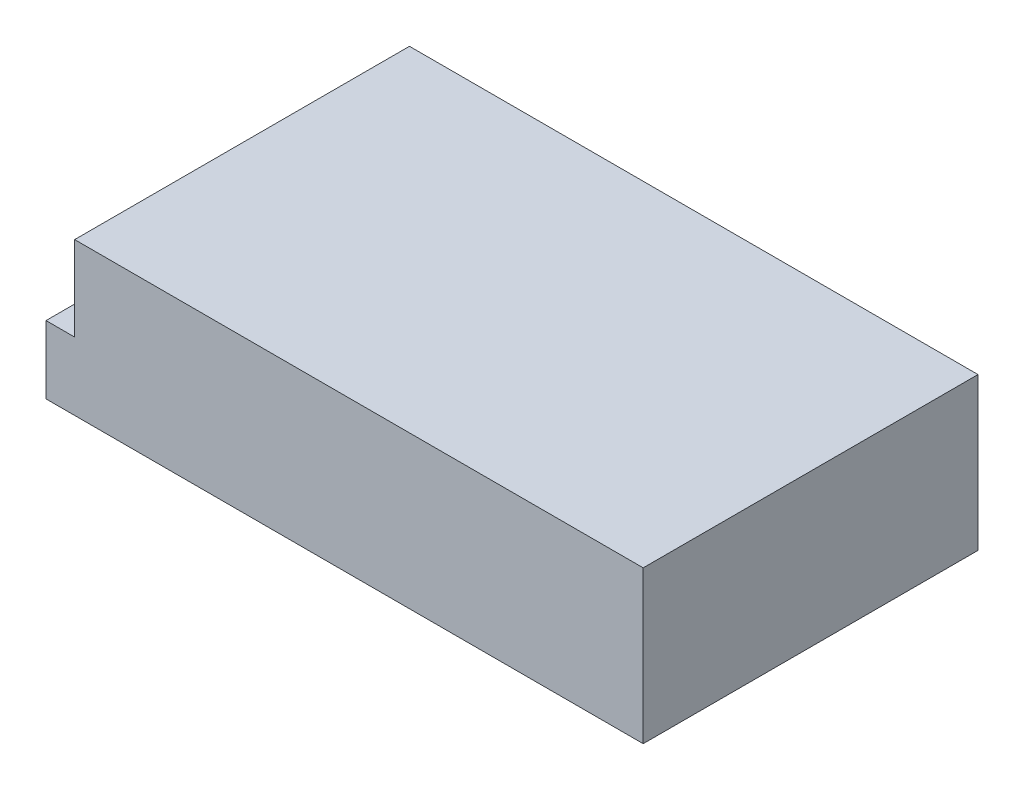
SolidWorks part; units mm, degrees
ref_plane "Front Plane" through (0, 0, 0) normal (0, 0, 1) x (1, 0, 0)
ref_plane "Top Plane" through (0, 0, 0) normal (0, 1, 0) x (1, 0, 0)
ref_plane "Right Plane" through (0, 0, 0) normal (1, 0, 0) x (0, 0, -1)
sketch "Sketch1" plane through (0, 0, 0) normal (0, 1, 0) x (1, 0, 0)
  line L0 (0, 41.5383) -> (0, -45.9656) construction
  line L1 (-99, 55.5) -> (99, 55.5)
  line L2 (-99, 55.5) -> (-99, -55.5)
  line L3 (-99, -55.5) -> (99, -55.5)
  line L4 (99, 55.5) -> (99, -55.5)
  line L5 (-77.8681, 0) -> (67.7114, 0) construction
  dimension "D1" = 198
  dimension "D2" = 111
extrude "Boss-Extrude1" add sketch "Sketch1" along normal blind 50.5
sketch "Sketch2" plane through (0, 0, -55.5) normal (0, 0, -1) x (-1, 0, 0)
  line L0 (-99, 50.5) -> (99, 50.5) construction
  line L1 (89.5, 50.5) -> (99, 50.5)
  line L2 (89.5, 50.5) -> (89.5, 22.5)
  line L3 (89.5, 22.5) -> (99, 22.5)
  line L4 (99, 50.5) -> (99, 22.5)
  line L5 (99, 50.5) -> (99, 0) construction
  dimension "D1" = 28
  dimension "D2" = 9.5
extrude "Cut-Extrude1" cut sketch "Sketch2" against normal blind 147.5
sketch "Sketch4" plane through (0, 0, 0) normal (0, -1, 0) x (1, 0, 0)
  line L0 (87, 68.5931) -> (87, -70.457) construction
  line L2 (99, 55.5) -> (99, -55.5) construction
  line L3 (108.8775, -45.5) -> (-114.4936, -45.5) construction
  line L4 (99, -55.5) -> (-99, -55.5) construction
  line L5 (111.0581, 39.5) -> (-119.8441, 39.5) construction
  line L6 (-99, 55.5) -> (99, 55.5) construction
  circle A0 centre (87, 39.5) radius 1.5
  circle A1 centre (87, -45.5) radius 1.5
  circle A2 centre (-39, 39.5) radius 1.5
  circle A3 centre (-39, -45.5) radius 1.5
  dimension "D3" = 3
  dimension "D1" = 12
  dimension "D2" = 10
  dimension "D4" = 16
  dimension "D5" = 126
extrude "Cut-Extrude2" cut sketch "Sketch4" against normal blind 3
